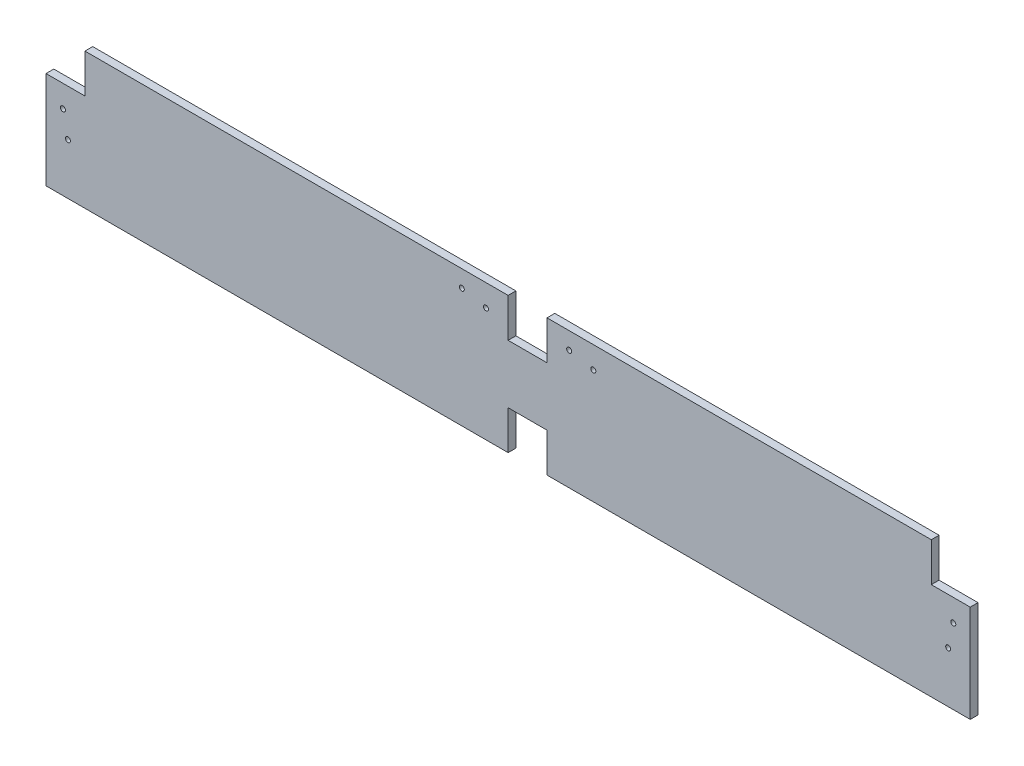
SolidWorks part; units mm, degrees
ref_plane "Front Plane" through (0, 0, 0) normal (0, 0, 1) x (1, 0, 0)
ref_plane "Top Plane" through (0, 0, 0) normal (0, 1, 0) x (1, 0, 0)
ref_plane "Right Plane" through (0, 0, 0) normal (1, 0, 0) x (0, 0, -1)
sketch "Sketch1" plane through (0, 0, 0) normal (0, 0, 1) x (1, 0, 0)
  line L1 (301.625, 44.45) -> (-301.625, 44.45)
  line L2 (301.625, 44.45) -> (301.625, -44.45)
  line L3 (301.625, -44.45) -> (-301.625, -44.45)
  line L4 (-301.625, 44.45) -> (-301.625, -44.45)
  line L5 (301.625, 44.45) -> (-301.625, -44.45) construction
  line L6 (301.625, -44.45) -> (-301.625, 44.45) construction
  point P0 (0, 0)
  dimension "D1" = 88.9
  dimension "D2" = 603.25
extrude "Boss-Extrude1" add sketch "Sketch1" along normal mid plane 5.08
sketch "Sketch2" plane through (0, 0, 2.54) normal (0, 0, 1) x (1, 0, 0)
  line L0 (301.625, 44.45) -> (-301.625, 44.45) construction
  line L1 (-301.625, 44.45) -> (-276.225, 44.45)
  line L2 (-301.625, 44.45) -> (-301.625, 19.05)
  line L3 (-301.625, 19.05) -> (-276.225, 19.05)
  line L4 (-276.225, 44.45) -> (-276.225, 19.05)
  line L9 (301.625, 44.45) -> (276.225, 44.45)
  line L10 (301.625, 44.45) -> (301.625, 19.05)
  line L11 (301.625, 19.05) -> (276.225, 19.05)
  line L12 (276.225, 44.45) -> (276.225, 19.05)
  line L13 (301.625, -44.45) -> (301.625, 44.45) construction
  line L14 (-301.625, -44.45) -> (301.625, -44.45) construction
  line L15 (0, 44.45) -> (25.4, 44.45)
  line L16 (0, 44.45) -> (0, 19.05)
  line L17 (0, 19.05) -> (25.4, 19.05)
  line L18 (25.4, 44.45) -> (25.4, 19.05)
  line L19 (0, -44.45) -> (25.4, -44.45)
  line L20 (0, -44.45) -> (0, -19.05)
  line L21 (0, -19.05) -> (25.4, -19.05)
  line L22 (25.4, -44.45) -> (25.4, -19.05)
  line L23 (0, 19.05) -> (0, -19.05) construction
  point P9 (0, 0)
  dimension "D1" = 25.4
extrude "Cut-Extrude1" cut sketch "Sketch2" against normal blind 5.08
sketch "Sketch3" plane through (0, 0, 2.54) normal (0, 0, 1) x (1, 0, 0)
  line L0 (12.7, 19.05) -> (12.7, 44.45) construction
  line L1 (0, 19.05) -> (25.4, 19.05) construction
  line L2 (-14.478, 30.099) -> (-14.478, 33.401) construction
  line L3 (0, 44.45) -> (0, 19.05) construction
  line L4 (0, 44.45) -> (-276.225, 44.45) construction
  circle A0 centre (-14.478, 30.099) radius 1.632
  circle A2 centre (-30.226, 33.401) radius 1.6319
  point P2 (-14.0009, 31.75)
  point P4 (12.7, 31.75)
  point P9 (-30.226, 32.8576)
  point P12 (0, 0)
  point P13 (-14.478, 34.6614)
  point P18 (-14.478, 31.75)
  point P19 (-30.226, 29.6224)
  point P20 (-14.478, 29.764)
  dimension "D1" = 3.2639
  dimension "D2" = 14.478
  dimension "D3" = 15.748
  dimension "D4" = 3.302
extrude "Cut-Extrude2" cut sketch "Sketch3" against normal blind 5.08
ref_plane "Plane1" through (12.7, 0, 0) normal (1, 0, 0) x (0, 0, -1)
sketch "Sketch4" plane through (0, 0, 2.54) normal (0, 0, 1) x (1, 0, 0)
  line L0 (-301.625, 15.381) -> (-276.225, 15.381) construction
  line L1 (-301.625, 19.05) -> (-301.625, -44.45) construction
  line L2 (-276.225, 19.05) -> (-276.225, 44.45) construction
  line L3 (-290.576, 4.572) -> (-287.274, 4.572) construction
  line L4 (-301.625, 19.05) -> (-276.225, 19.05) construction
  circle A0 centre (-290.576, 4.572) radius 1.632
  circle A1 centre (-287.274, -11.176) radius 1.632
  point P10 (-288.925, 4.572)
  point P12 (-288.925, 15.381)
  point P13 (-288.1333, -5.8812)
  point P14 (0, 0)
  point P15 (-290.576, 8.9124)
  dimension "D1" = 3.2639
  dimension "D2" = 3.302
  dimension "D3" = 15.748
  dimension "D4" = 14.478
extrude "Cut-Extrude3" cut sketch "Sketch4" against normal blind 5.08
mirror "Mirror2" about plane through (0, 0, 0) normal (1, 0, 0) of "Cut-Extrude3"
pattern_linear "LPattern1" count 2 spacing 70.104 along (1, 0, 0) of "Cut-Extrude2"
